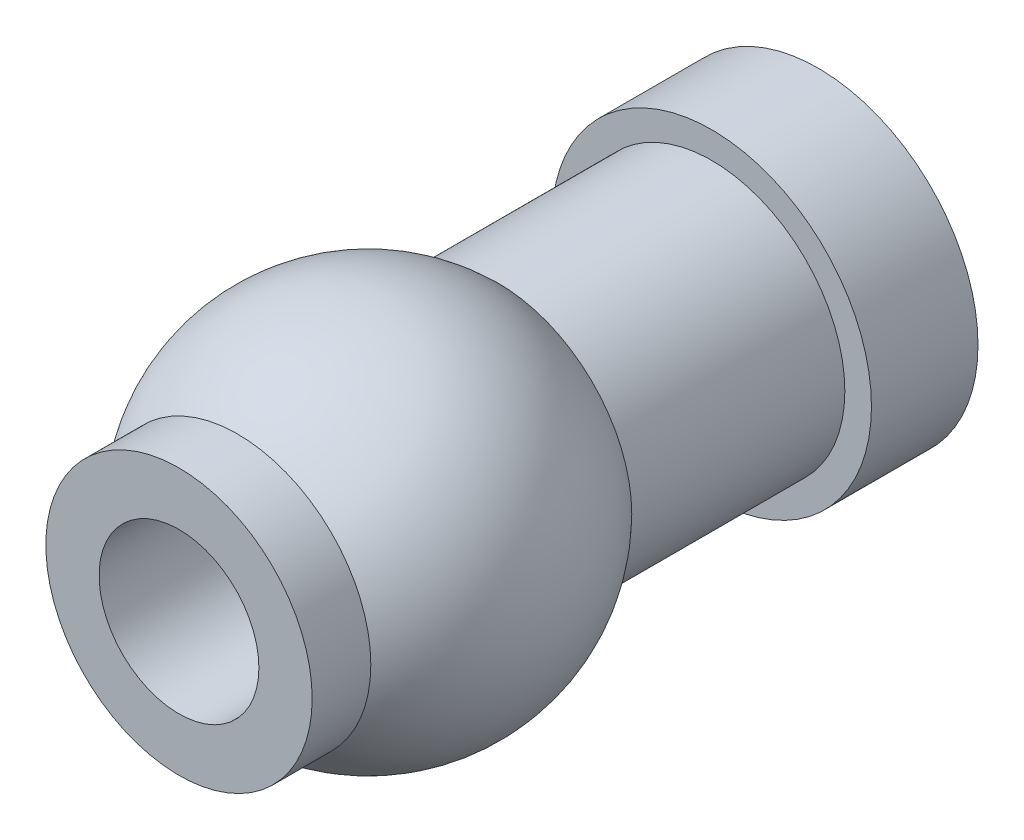
SolidWorks part; units mm, degrees
material "1060 Alloy"
ref_plane "Front Plane" through (0, 0, 0) normal (0, 0, 1) x (1, 0, 0)
ref_plane "Top Plane" through (0, 0, 0) normal (0, 1, 0) x (1, 0, 0)
ref_plane "Right Plane" through (0, 0, 0) normal (1, 0, 0) x (0, 0, -1)
sketch "Sketch1" plane through (0, 0, 0) normal (1, 0, 0) x (0, 0, -1)
  line L0 (0, 0) -> (12, 0) construction
  line L1 (12, 1.5) -> (12, 3)
  line L2 (12, 3) -> (10, 3)
  line L3 (10, 3) -> (10, 2.5)
  line L4 (10, 2.5) -> (6, 2.5)
  line L5 (12, 1.5) -> (0, 1.5)
  line L6 (0, 1.5) -> (0, 2.5)
  line L7 (0, 2.5) -> (1.101, 2.5)
  circle A0 centre (3.5505, 0) radius 3.5
  dimension "D1" = 7
  dimension "D2" = 3
  dimension "D3" = 2.5
  dimension "D4" = 2
  dimension "D5" = 4
  dimension "D6" = 1.5
  dimension "D7" = 1
  dimension "D8" = 12
revolve "Revolve1" add sketch "Sketch1" angle 360 about L0
